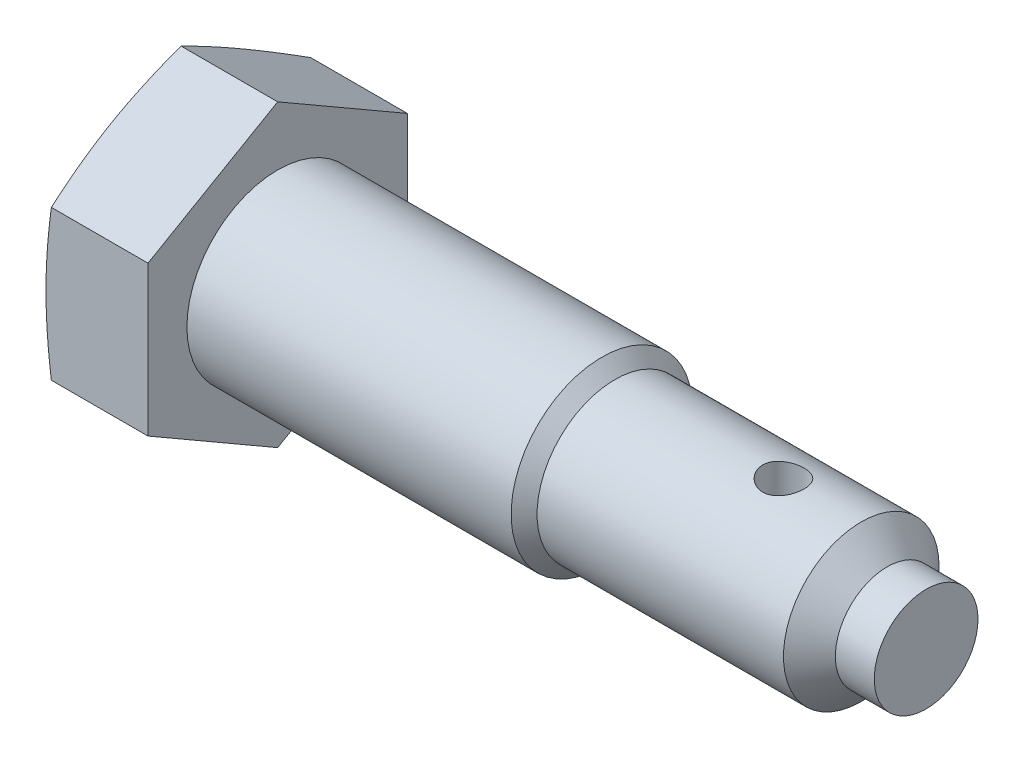
SolidWorks part; units mm, degrees
ref_plane "Плоскость1" through (0, 0, 0) normal (0, 0, 1) x (1, 0, 0)
ref_plane "Плоскость2" through (0, 0, 0) normal (0, 1, 0) x (1, 0, 0)
ref_plane "Плоскость3" through (0, 0, 0) normal (1, 0, 0) x (0, 0, -1)
sketch "BodySke" plane through (0, 0, 0) normal (0, 0, 1) x (1, 0, 0)
  line L0 (0, 0) -> (-13.929, 0) construction
  line L1 (0, 0) -> (0, 3.5)
  line L2 (0, 3.5) -> (12.5, 3.5)
  line L3 (12.5, 3.5) -> (13, 3)
  line L4 (13, 3) -> (22.5, 3)
  line L5 (22.5, 3) -> (23.5, 2)
  line L6 (23.5, 2) -> (25, 2)
  line L7 (25, 2) -> (25, 0)
  line L8 (25, 0) -> (0, 0)
  dimension "D1" = 7
  dimension "Diameter" = 6
  dimension "D2" = 4
  dimension "L2" = 13
  dimension "L3" = 1.5
  dimension "D7" = 45
  dimension "D8" = 45
  dimension "Length" = 25
revolve "BaseBody" add sketch "BodySke" angle 360 about L0
cosmetic thread "ThreadCosmetic"
sketch "Ske" plane through (0, 0, 0) normal (-1, 0, 0) x (0, 0, 1)
  line L1 (0, 5.7735) -> (-5, 2.8868)
  line L2 (-5, 2.8868) -> (-5, -2.8868)
  line L3 (-5, -2.8868) -> (0, -5.7735)
  line L4 (0, -5.7735) -> (5, -2.8868)
  line L5 (5, -2.8868) -> (5, 2.8868)
  line L6 (5, 2.8868) -> (0, 5.7735)
  circle A0 centre (0, 0) radius 5 construction
  dimension "Width_Flats" = 10
extrude "BaseHead" add sketch "Ske" along normal blind 4
sketch "Ske1" plane through (0, 0, 0) normal (0, 0, 1) x (1, 0, 0)
  line L0 (0, 0) -> (-7.7485, 0) construction
  line L1 (0, 0) -> (-13.929, 0) construction
  line L2 (-4, 5.7735) -> (0, 5.7735) construction
  line L3 (-4, 2.8868) -> (-4, 5.7735) construction
  line L4 (-4, 5.7735) -> (-3.7258, 5.7735)
  line L5 (-4, 4.75) -> (-4, 5.7735)
  line L6 (-3.7258, 5.7735) -> (-4, 4.75)
  dimension "D1" = 9.5
  dimension "Head_ch_ang" = 15
revolve "HeadFillet" cut sketch "Ske1" angle 360 about L0
sketch "Ske2" plane through (0, 0, 0) normal (0, 1, 0) x (1, 0, 0)
  line L0 (0, -5) -> (0, 0) construction
  line L1 (-3.7258, 0) -> (0, 0) construction
  circle A0 centre (19.5, 0) radius 0.8
  dimension "D3" = 1.6
  dimension "LContr" = 19.5
extrude "Hole" cut sketch "Ske2" against normal through all and the other way through all
equation "\"D1@Ske1\" = .95 * \"Width_Flats@Ske\""
